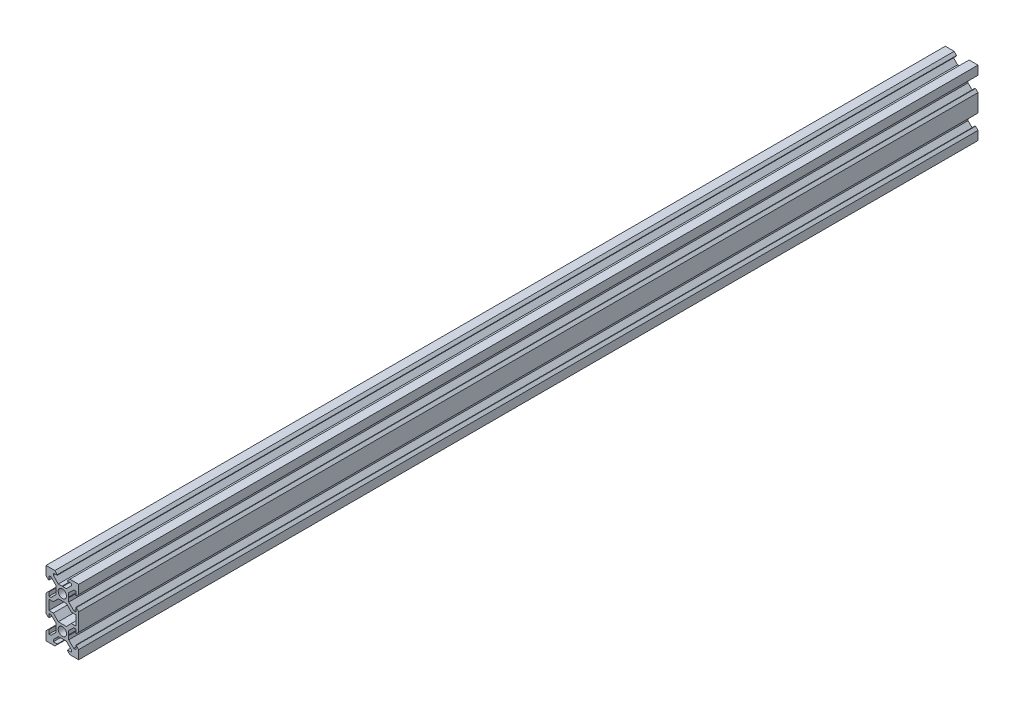
SolidWorks part; units mm, degrees
ref_plane "Спереди" through (0, 0, 0) normal (0, 0, 1) x (1, 0, 0)
ref_plane "Сверху" through (0, 0, 0) normal (0, 1, 0) x (1, 0, 0)
ref_plane "Справа" through (0, 0, 0) normal (1, 0, 0) x (0, 0, -1)
ref_plane "Плоскость4" through (0, 0, 792.9) normal (0, 0, 1) x (1, 0, 0)
sketch "Эскиз1" plane through (0, 0, 792.9) normal (0, 0, 1) x (1, 0, 0)
  line L0 (-2.4781, -3.9) -> (2.4781, -3.9)
  line L1 (2.4781, -3.9) -> (5.5, -7.002)
  line L2 (5.5, -7.002) -> (8.2, -7.002)
  line L3 (8.2, -7.002) -> (8.2, -12.998)
  line L4 (8.2, -12.998) -> (5.5, -12.998)
  line L5 (5.5, -12.998) -> (2.4781, -16.1)
  line L6 (2.4781, -16.1) -> (-2.4781, -16.1)
  line L7 (-2.4781, -16.1) -> (-5.5, -12.998)
  line L8 (-5.5, -12.998) -> (-8.2, -12.998)
  line L9 (-8.2, -12.998) -> (-8.2, -7.002)
  line L10 (-8.2, -7.002) -> (-5.5, -7.002)
  line L11 (-5.5, -7.002) -> (-2.4781, -3.9)
  line L12 (-8.2, -3.125) -> (-8.5064, -3.125)
  line L13 (-8.5064, -3.125) -> (-10, -4.58)
  line L14 (-10, -4.58) -> (-10, -15.42)
  line L15 (-10, -15.42) -> (-8.5064, -16.875)
  line L16 (-8.5064, -16.875) -> (-8.2, -16.875)
  line L17 (-8.2, -16.875) -> (-8.2, -14.5)
  line L18 (-8.2, -14.5) -> (-7.002, -14.5)
  line L19 (-7.002, -14.5) -> (-3.9, -17.5219)
  line L20 (-3.9, -17.5219) -> (-3.9, -19.8)
  line L21 (-3.9, -19.8) -> (-3.7, -20)
  line L22 (-3.7, -20) -> (-3.9, -20.2)
  line L23 (-3.9, -20.2) -> (-3.9, -22.4781)
  line L24 (-3.9, -22.4781) -> (-7.002, -25.5)
  line L25 (-7.002, -25.5) -> (-8.2, -25.5)
  line L26 (-8.2, -25.5) -> (-8.2, -23.125)
  line L27 (-8.2, -23.125) -> (-8.5064, -23.125)
  line L28 (-8.5064, -23.125) -> (-10, -24.58)
  line L29 (-10, -24.58) -> (-10, -30)
  line L30 (-10, -30) -> (-4.58, -30)
  line L31 (-4.58, -30) -> (-3.125, -28.5064)
  line L32 (-3.125, -28.5064) -> (-3.125, -28.2)
  line L33 (-3.125, -28.2) -> (-5.5, -28.2)
  line L34 (-5.5, -28.2) -> (-5.5, -27.002)
  line L35 (-5.5, -27.002) -> (-2.4781, -23.9)
  line L36 (-2.4781, -23.9) -> (-0.2, -23.9)
  line L37 (-0.2, -23.9) -> (0, -23.7)
  line L38 (0, -23.7) -> (0.2, -23.9)
  line L39 (0.2, -23.9) -> (2.4781, -23.9)
  line L40 (2.4781, -23.9) -> (5.5, -27.002)
  line L41 (5.5, -27.002) -> (5.5, -28.2)
  line L42 (5.5, -28.2) -> (3.125, -28.2)
  line L43 (3.125, -28.2) -> (3.125, -28.5064)
  line L44 (3.125, -28.5064) -> (4.58, -30)
  line L45 (4.58, -30) -> (10, -30)
  line L46 (10, -30) -> (10, -24.58)
  line L47 (10, -24.58) -> (8.5064, -23.125)
  line L48 (8.5064, -23.125) -> (8.2, -23.125)
  line L49 (8.2, -23.125) -> (8.2, -25.5)
  line L50 (8.2, -25.5) -> (7.002, -25.5)
  line L51 (7.002, -25.5) -> (3.9, -22.4781)
  line L52 (3.9, -22.4781) -> (3.9, -20.2)
  line L53 (3.9, -20.2) -> (3.7, -20)
  line L54 (3.7, -20) -> (3.9, -19.8)
  line L55 (3.9, -19.8) -> (3.9, -17.5219)
  line L56 (3.9, -17.5219) -> (7.002, -14.5)
  line L57 (7.002, -14.5) -> (8.2, -14.5)
  line L58 (8.2, -14.5) -> (8.2, -16.875)
  line L59 (8.2, -16.875) -> (8.5064, -16.875)
  line L60 (8.5064, -16.875) -> (10, -15.42)
  line L61 (10, -15.42) -> (10, -4.58)
  line L62 (10, -4.58) -> (8.5064, -3.125)
  line L63 (8.5064, -3.125) -> (8.2, -3.125)
  line L64 (8.2, -3.125) -> (8.2, -5.5)
  line L65 (8.2, -5.5) -> (7.002, -5.5)
  line L66 (7.002, -5.5) -> (3.9, -2.4781)
  line L67 (3.9, -2.4781) -> (3.9, -0.2)
  line L68 (3.9, -0.2) -> (3.7, 0)
  line L69 (3.7, 0) -> (3.9, 0.2)
  line L70 (3.9, 0.2) -> (3.9, 2.4781)
  line L71 (3.9, 2.4781) -> (7.002, 5.5)
  line L72 (7.002, 5.5) -> (8.2, 5.5)
  line L73 (8.2, 5.5) -> (8.2, 3.125)
  line L74 (8.2, 3.125) -> (8.5064, 3.125)
  line L75 (8.5064, 3.125) -> (10, 4.58)
  line L76 (10, 4.58) -> (10, 10)
  line L77 (10, 10) -> (4.58, 10)
  line L78 (4.58, 10) -> (3.125, 8.5064)
  line L79 (3.125, 8.5064) -> (3.125, 8.2)
  line L80 (3.125, 8.2) -> (5.5, 8.2)
  line L81 (5.5, 8.2) -> (5.5, 7.002)
  line L82 (5.5, 7.002) -> (2.4781, 3.9)
  line L83 (2.4781, 3.9) -> (0.2, 3.9)
  line L84 (0.2, 3.9) -> (0, 3.7)
  line L85 (0, 3.7) -> (-0.2, 3.9)
  line L86 (-0.2, 3.9) -> (-2.4781, 3.9)
  line L87 (-2.4781, 3.9) -> (-5.5, 7.002)
  line L88 (-5.5, 7.002) -> (-5.5, 8.2)
  line L89 (-5.5, 8.2) -> (-3.125, 8.2)
  line L90 (-3.125, 8.2) -> (-3.125, 8.5064)
  line L91 (-3.125, 8.5064) -> (-4.58, 10)
  line L92 (-4.58, 10) -> (-10, 10)
  line L93 (-10, 10) -> (-10, 4.58)
  line L94 (-10, 4.58) -> (-8.5064, 3.125)
  line L95 (-8.5064, 3.125) -> (-8.2, 3.125)
  line L96 (-8.2, 3.125) -> (-8.2, 5.5)
  line L97 (-8.2, 5.5) -> (-7.002, 5.5)
  line L98 (-7.002, 5.5) -> (-3.9, 2.4781)
  line L99 (-3.9, 2.4781) -> (-3.9, 0.2)
  line L100 (-3.9, 0.2) -> (-3.7, 0)
  line L101 (-3.7, 0) -> (-3.9, -0.2)
  line L102 (-3.9, -0.2) -> (-3.9, -2.4781)
  line L103 (-3.9, -2.4781) -> (-7.002, -5.5)
  line L104 (-7.002, -5.5) -> (-8.2, -5.5)
  line L105 (-8.2, -5.5) -> (-8.2, -3.125)
  circle A0 centre (0, 0) radius 2.55
  circle A1 centre (0, -20) radius 2.55
extrude "Бобышка-Вытянуть1" add sketch "Эскиз1" against normal blind 550
